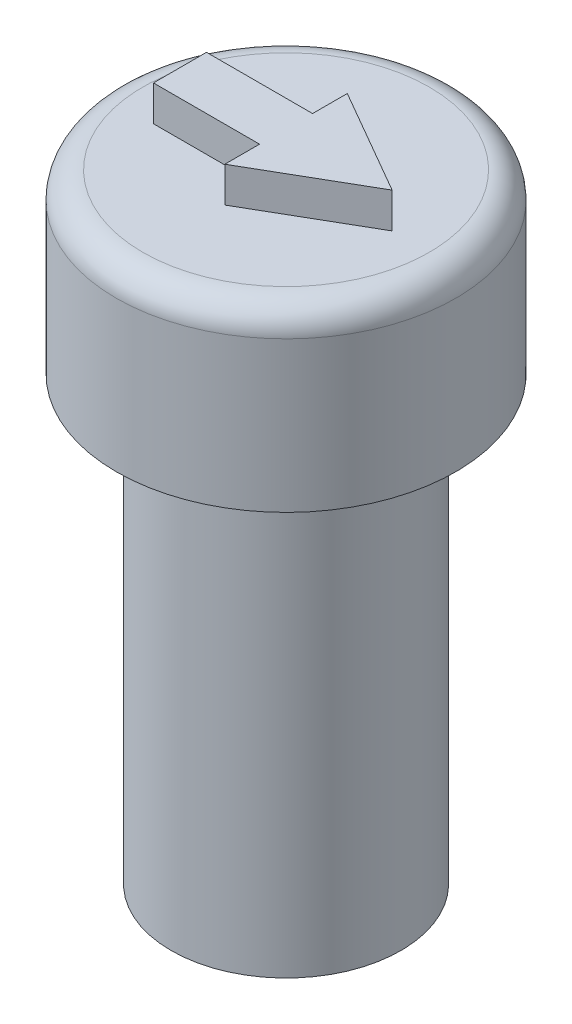
SolidWorks part; units mm, degrees
ref_plane "Front Plane" through (0, 0, 0) normal (0, 0, 1) x (1, 0, 0)
ref_plane "Top Plane" through (0, 0, 0) normal (0, 1, 0) x (1, 0, 0)
ref_plane "Right Plane" through (0, 0, 0) normal (1, 0, 0) x (0, 0, -1)
sketch "Sketch1" plane through (0, 0, 0) normal (0, 1, 0) x (1, 0, 0)
  circle A0 centre (0, 0) radius 3.25
  dimension "D1" = 6.5
extrude "Boss-Extrude1" add sketch "Sketch1" along normal blind 12.5 contours A0
sketch "Sketch2" plane through (0, 0, 0) normal (0, -1, 0) x (1, 0, 0)
  circle A1 centre (0, 0) radius 1.75
  dimension "D1" = 3.5
extrude "Cut-Extrude1" cut sketch "Sketch2" against normal blind 2.5
sketch "Sketch6" plane through (0, 12.5, 0) normal (0, 1, 0) x (1, 0, 0)
  circle A0 centre (0, 0) radius 4.8
  dimension "D1" = 9.6
extrude "Boss-Extrude2" add sketch "Sketch6" along normal blind 5 contours A0
fillet "Fillet1" radius 0.75 1 edges at (0, 17.5, 4.8)
sketch "Sketch7" plane through (0, 17.5, 0) normal (0, 1, 0) x (1, 0, 0)
  line L0 (0, 0) -> (-3, 0) construction
  line L1 (0, 0) -> (1, 0) construction
  line L2 (0, 0) -> (1, 0) construction
  line L3 (3, 0) -> (0, 1.7321)
  line L4 (0, 1.7321) -> (0, -1.7321)
  line L5 (0, -1.7321) -> (3, 0)
  line L6 (1, 0) -> (3, 0) construction
  line L7 (-3, 0) -> (-3, 0.75)
  line L8 (-3, 0.75) -> (0, 0.75)
  line L9 (0, 0.75) -> (0, -0.75)
  line L10 (0, -0.75) -> (-3, -0.75)
  line L11 (-3, -0.75) -> (-3, 0)
  circle A0 centre (1, 0) radius 1 construction
  dimension "D1" = 1
  dimension "D2" = 2
  dimension "D3" = 3
  dimension "D4" = 0.75
  dimension "D5" = 0.75
sketch "Sketch8" plane through (0, 17.5, 0) normal (0, 1, 0) x (1, 0, 0)
  line L0 (0, 0.75) -> (-3, 0.75)
  line L1 (-3, 0.75) -> (-3, -0.75)
  line L2 (-3, -0.75) -> (0, -0.75)
  line L3 (0, -0.75) -> (0, -1.7321)
  line L4 (0, -1.7321) -> (3, 0)
  line L5 (3, 0) -> (0, 1.7321)
  line L6 (0, 1.7321) -> (0, 0.75)
extrude "Boss-Extrude3" add sketch "Sketch8" along normal blind 1
